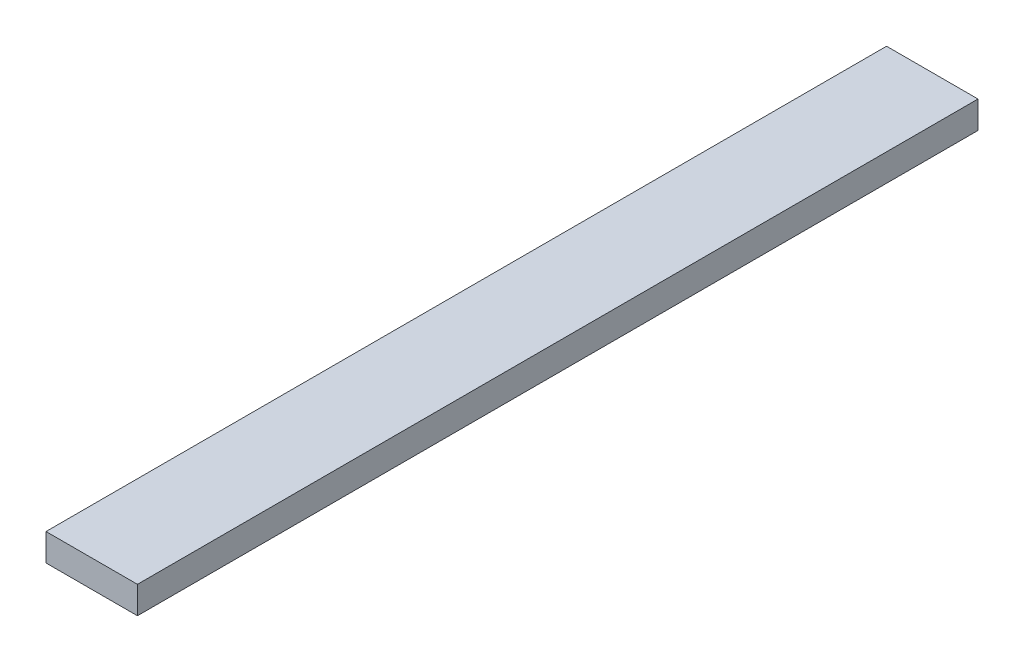
SolidWorks part; units mm, degrees
ref_plane "Plan de face" through (0, 0, 0) normal (0, 0, 1) x (1, 0, 0)
ref_plane "Plan de dessus" through (0, 0, 0) normal (0, 1, 0) x (1, 0, 0)
ref_plane "Plan de droite" through (0, 0, 0) normal (1, 0, 0) x (0, 0, -1)
sketch "Esquisse1" plane through (0, 0, 0) normal (0, 0, 1) x (1, 0, 0)
  line L1 (-10.0623, 3) -> (10.0623, 3)
  line L2 (-10.0623, 3) -> (-10.0623, -3)
  line L3 (-10.0623, -3) -> (10.0623, -3)
  line L4 (10.0623, 3) -> (10.0623, -3)
  dimension "D1" = 21
  dimension "D2" = 6
  dimension "D3" = 20.1246
  dimension "D4" = 10.0623
  dimension "D5" = 3
extrude "Boss.-Extru.1" add sketch "Esquisse1" along normal blind 185
equation "\"D5@Esquisse1\"=\"D2@Esquisse1\"/2"
equation "\"D4@Esquisse1\"=\"D3@Esquisse1\"/2"
